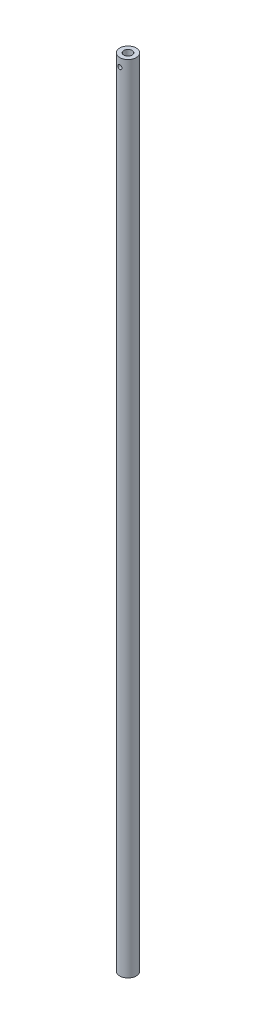
SolidWorks part; units mm, degrees
material "6061-T6 (SS)"
ref_plane "Front Plane" through (0, 0, 0) normal (0, 0, 1) x (1, 0, 0)
ref_plane "Top Plane" through (0, 0, 0) normal (0, 1, 0) x (1, 0, 0)
ref_plane "Right Plane" through (0, 0, 0) normal (1, 0, 0) x (0, 0, -1)
sketch "Sketch1" plane through (0, 0, 0) normal (0, 1, 0) x (1, 0, 0)
  circle A0 centre (0, 0) radius 12.7
  circle A1 centre (0, 0) radius 6.35
  dimension "D1" = 25.4
  dimension "D2" = 6.35
extrude "Boss-Extrude2" add sketch "Sketch1" along normal blind 1219.2
ref_plane "Plane1" through (0, 0, 25.4) normal (0, 0, 1) x (1, 0, 0)
sketch "Sketch2" plane through (0, 0, 25.4) normal (0, 0, 1) x (1, 0, 0)
  line L0 (12.7, 1219.2) -> (-12.7, 1219.2) construction
  line L1 (12.7, 0) -> (12.7, 1219.2) construction
  circle A0 centre (0, 1206.5) radius 3.175
  dimension "D1" = 6.35
  dimension "D2" = 12.7
  dimension "D3" = 12.7
extrude "Cut-Extrude1" cut sketch "Sketch2" against normal through all
equation "\"ScopeLengthUnit\"= 10 * \"ScaleFactor\""
equation "\"EyepieceRadius\"= 0.75 * \"ScaleFactor\""
equation "\"ScopeThickness\"= 0.1 * \"ScaleFactor\""
equation "\"ScopeLensWidth\"= 2 * \"ScaleFactor\""
equation "\"ScopeOutsideRadius\"= 2.1 * \"ScaleFactor\""
equation "\"PegWidth\"=1"
equation "\"SupportOutsideDiam\"= \"ScopeOutsideRadius\" * 2 + .25"
equation "\"RotatingDiskDiam\"=3"
equation "\"LegSeatWidth\"=4 "
equation "\"LegSeatHeight\"=2"
equation "\"D1@Sketch1\"=\"LegSeatWidth\"/4"
equation "\"LegThickness\"=0.25"
equation "\"D2@Sketch1\"=\"LegThickness\""
equation "\"LegHeight\"=48"
equation "\"D1@Boss-Extrude2\"=\"LegHeight\""
equation "\"RotatingDiskHousingDiameter\"= (\"RotatingDiskDiam\" + 2)"
equation "\"BoltCircleDiam\"= ( \"RotatingDiskDiam\" + \"RotatingDiskHousingDiameter\" ) / 2"
equation "\"LegBoltDiam\"=0.25"
equation "\"D1@Sketch2\"=\"LegBoltDiam\""
equation "\"D2@Sketch2\"=\"LegSeatWidth\"/8"
equation "\"D3@Sketch2\"=\"LegSeatWidth\"/8"
equation "\"PinHeight\"=\"RotDiskLidHeight\" + \"RotDiskHeight\" + \"PinBoltDiam\"*3"
equation "\"PinBoltDiam\"=0.25"
equation "\"RotDiskHeight\"=0.5"
equation "\"RotDiskLidHeight\"= 0.5"
equation "\"DiskSeatPinDiam\"=0.25"
equation "\"ScaleFactor\"= 1"
